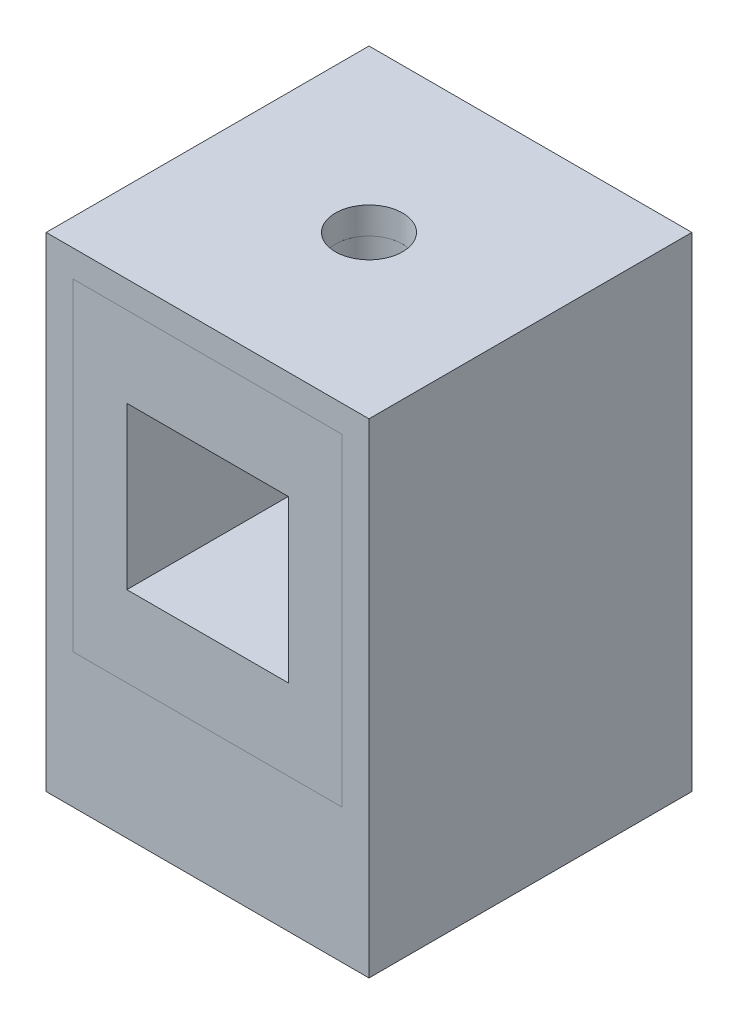
SolidWorks part; units mm, degrees
ref_plane "Front Plane" through (0, 0, 0) normal (0, 0, 1) x (1, 0, 0)
ref_plane "Top Plane" through (0, 0, 0) normal (0, 1, 0) x (1, 0, 0)
ref_plane "Right Plane" through (0, 0, 0) normal (1, 0, 0) x (0, 0, -1)
sketch "Sketch1" plane through (0, 0, 0) normal (0, 1, 0) x (1, 0, 0)
  line L0 (0, -152.4) -> (0, 0) construction
  line L1 (-152.4, 152.4) -> (152.4, 152.4)
  line L2 (-152.4, 152.4) -> (-152.4, -152.4)
  line L3 (-152.4, -152.4) -> (152.4, -152.4)
  line L4 (152.4, 152.4) -> (152.4, -152.4)
  line L5 (0, 0) -> (152.4, 0) construction
  dimension "D1" = 304.8
  dimension "D2" = 304.8
extrude "Extrude1" add sketch "Sketch1" against normal blind 457.2
sketch "Sketch2" plane through (0, 0, 152.4) normal (0, 0, 1) x (1, 0, 0)
  line L0 (0, -330.2) -> (0, 0) construction
  line L1 (-127, -25.4) -> (127, -25.4)
  line L2 (-127, -25.4) -> (-127, -330.2)
  line L3 (-127, -330.2) -> (127, -330.2)
  line L4 (127, -25.4) -> (127, -330.2)
  line L5 (-152.4, 0) -> (152.4, 0) construction
  dimension "D1" = 304.8
  dimension "D2" = 254
  dimension "D3" = 25.4
extrude "Extrude2" cut sketch "Sketch2" against normal offset from surface (279.4 mm away) 25.4 up to face at (0, -228.6, -152.4)
sketch "Sketch3" plane through (0, 0, 152.4) normal (0, 0, 1) x (1, 0, 0)
  line L1 (-127, -25.4) -> (127, -25.4)
  line L2 (-127, -25.4) -> (-127, -330.2)
  line L3 (-127, -330.2) -> (127, -330.2)
  line L4 (127, -25.4) -> (127, -330.2)
extrude "Extrude3" add sketch "Sketch3" against normal up to next separate body
sketch "Sketch4" plane through (0, 0, 152.4) normal (0, 0, 1) x (1, 0, 0)
  line L0 (0, -101.6) -> (0, 0) construction
  line L1 (-76.2, -254) -> (76.2, -254)
  line L2 (-76.2, -254) -> (-76.2, -101.6)
  line L3 (-76.2, -101.6) -> (76.2, -101.6)
  line L4 (76.2, -254) -> (76.2, -101.6)
  line L5 (76.2, -177.8) -> (127, -177.8) construction
  line L6 (127, -330.2) -> (127, -25.4) construction
  dimension "D1" = 152.4
  dimension "D2" = 152.4
extrude "Extrude4" cut sketch "Sketch4" against normal blind 254
sketch "Sketch5" plane through (0, 0, 0) normal (0, 1, 0) x (1, 0, 0)
  circle A0 centre (0, 0) radius 31.75
  dimension "D1" = 63.5
extrude "Extrude5" cut sketch "Sketch5" against normal up to surface (254 mm away) up to face at (0, -254, 25.4)
